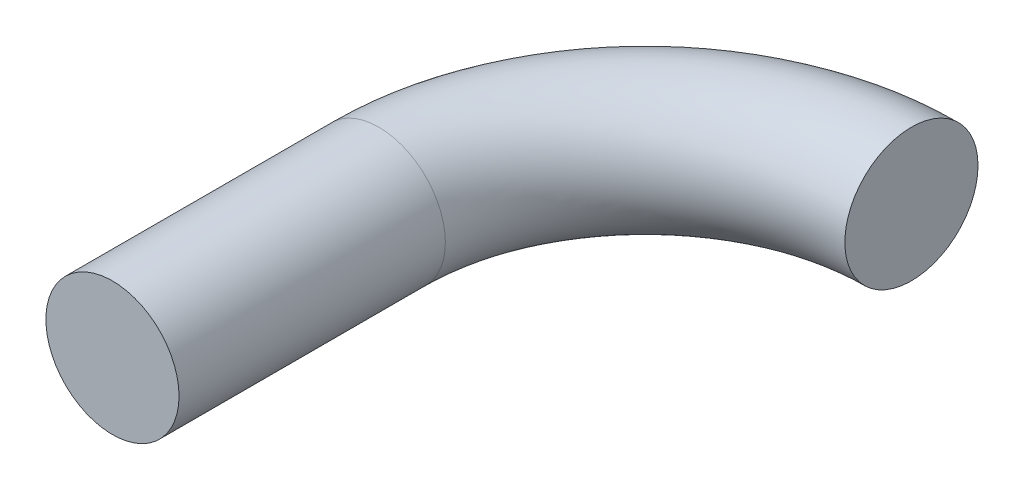
SolidWorks part; units mm, degrees
ref_plane "Front Plane" through (0, 0, 0) normal (0, 0, 1) x (1, 0, 0)
ref_plane "Top Plane" through (0, 0, 0) normal (0, 1, 0) x (1, 0, 0)
ref_plane "Right Plane" through (0, 0, 0) normal (1, 0, 0) x (0, 0, -1)
sketch "Sketch1" plane through (0, 0, 0) normal (0, 0, 1) x (1, 0, 0)
  circle A0 centre (0, 0) radius 12.7
  dimension "D1" = 25.4
sketch "Sketch2" plane through (0, 0, 0) normal (0, 1, 0) x (1, 0, 0)
  line L0 (0, 0) -> (0, 50.8)
  arc A0 (0, 50.8) -> (50.8, 101.6) centre (50.8, 50.8) cw
  dimension "D2" = 50.8
  dimension "D1" = 50.8
sweep "Sweep1" add profiles "Sketch1" path "Sketch2"
